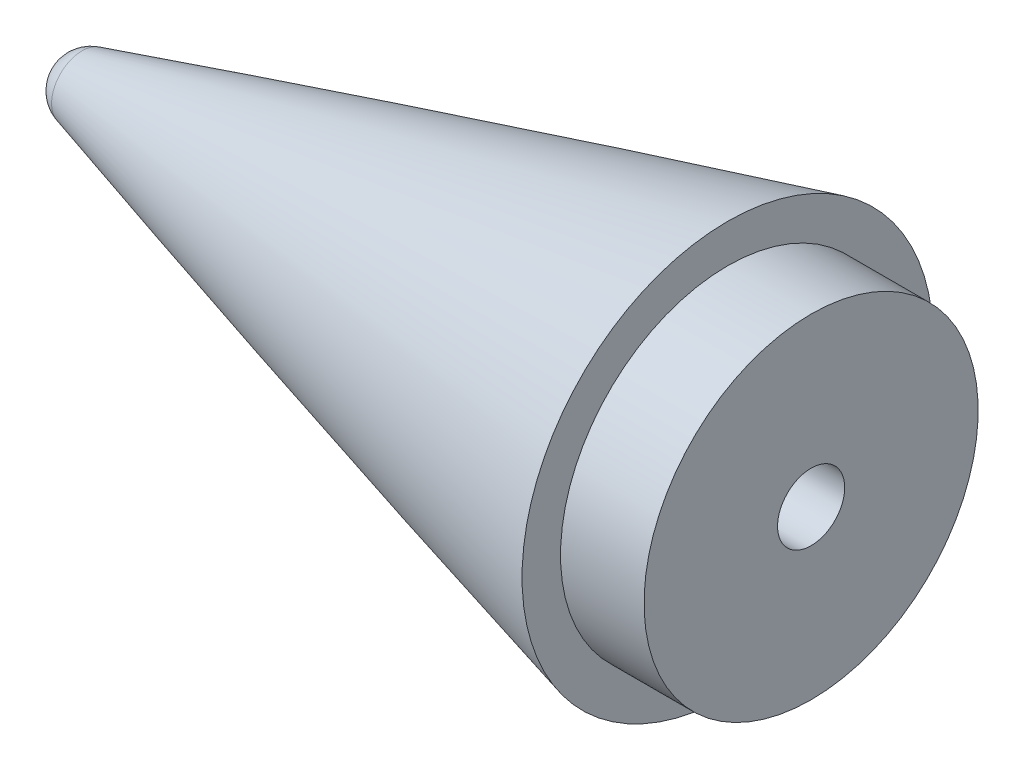
SolidWorks part; units mm, degrees
material "6061 Alloy"
ref_plane "Front Plane" through (0, 0, 0) normal (0, 0, 1) x (1, 0, 0)
ref_plane "Top Plane" through (0, 0, 0) normal (0, 1, 0) x (1, 0, 0)
ref_plane "Right Plane" through (0, 0, 0) normal (1, 0, 0) x (0, 0, -1)
sketch "Sketch1" plane through (0, 0, 0) normal (0, 0, 1) x (1, 0, 0)
  line L0 (-596.9, 0) -> (-647.7219, 0)
  line L1 (0, 0) -> (0, 78.359) construction
  line L2 (0, 78.359) -> (-101.6, 78.359) construction
  line L3 (-596.9, 0) -> (-596.9, 15.6253)
  line L4 (0, 0) -> (-596.9, 0) construction
  line L5 (-647.7219, 0) -> (-647.7219, 15.6253) construction
  line L6 (-647.7219, 0) -> (-654.05, 0) construction
  arc A0 (-596.9, 15.6253) -> (-645.9701, 2.3206) centre (-101.6, -1908.2739) ccw
  arc A1 (-101.6, 78.359) -> (-596.9, 15.6253) centre (-101.6, -1908.2739) ccw construction
  arc A2 (-645.9701, 2.3206) -> (-647.7219, 0) centre (-645.3089, 0) ccw
  arc A3 (-647.7219, 1.8206) -> (-654.05, 0) centre (-101.6, -1908.2739) ccw construction
  arc A4 (-645.9701, 2.3206) -> (-647.7219, 1.8206) centre (-101.6, -1908.2739) ccw construction
  point P11 (-648.8311, -4.6205)
  point P13 (0, 0)
  dimension "D5" = 2.413
  dimension "D1" = 78.359
  dimension "D2" = 101.6
  dimension "D3" = 654.05
  dimension "D4" = 57.15
revolve "Revolve2" add sketch "Sketch1" angle 360 about L4
sketch "Sketch2" plane through (-596.9, 0, 0) normal (1, 0, 0) x (0, 0, -1)
  circle A0 centre (0, 0) radius 12.7
  dimension "D1" = 25.4
extrude "Boss-Extrude1" add sketch "Sketch2" along normal blind 6.35
sketch "Sketch3" plane through (-590.55, 0, 0) normal (1, 0, 0) x (0, 0, -1)
  point P0 (0, 0)
hole_wizard "Tap Drill for 1/4-20 Tap1" positions "Sketch3" profile "Sketch4" hole size "1/4-20" standard "ANSI Inch"
sketch "Sketch4" plane through (-590.55, 0, 0) normal (0, 1, 0) x (0, 0, -1)
  line L0 (0, 0) -> (0, 26.9338)
  line L1 (0, 26.9338) -> (2.5527, 25.4)
  line L2 (2.5527, 25.4) -> (2.5527, 0)
  line L5 (2.5527, 0) -> (0, 0)
  line L10 (0, 26.9338) -> (-2.5527, 25.4) construction
  line L11 (0, -6.35) -> (0, 107.95) construction
  dimension "Hole Dia." = 5.1054
  dimension "Hole Depth" = 25.4
  dimension "Drill Angle" = 118
